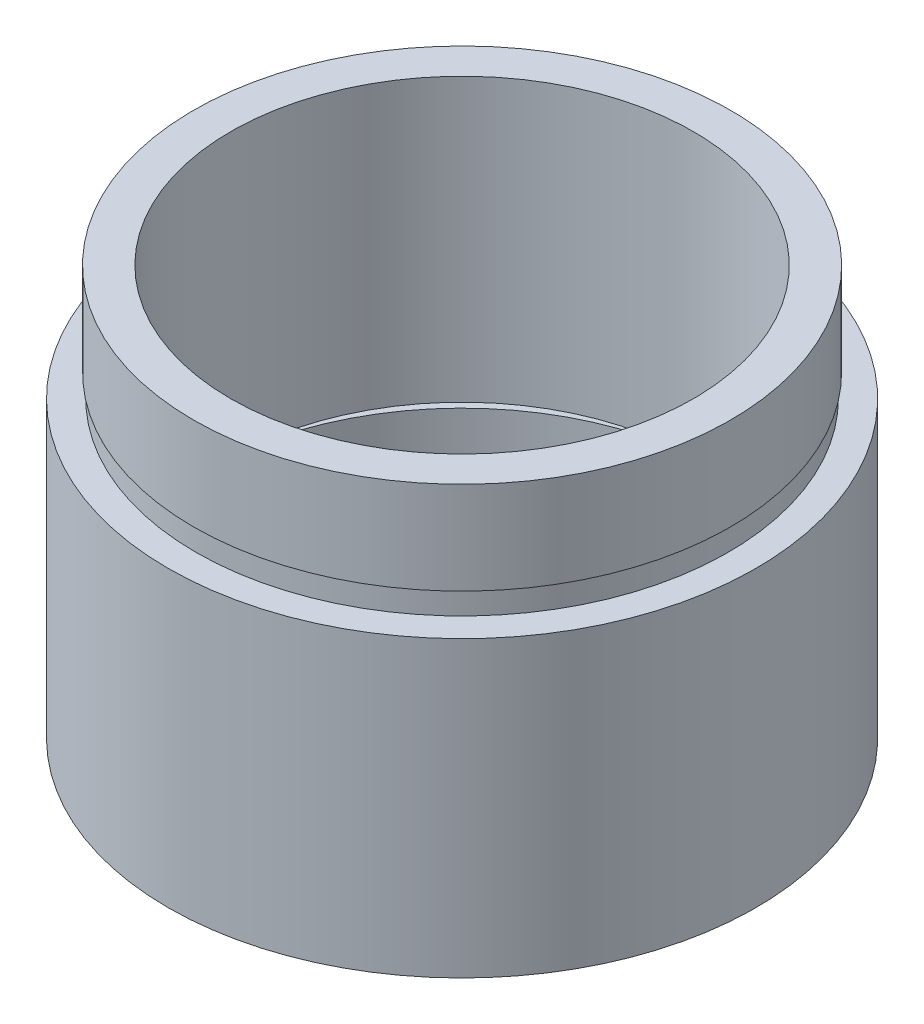
SolidWorks part; units mm, degrees
ref_plane "前视基准面" through (0, 0, 0) normal (0, 0, 1) x (1, 0, 0)
ref_plane "上视基准面" through (0, 0, 0) normal (0, 1, 0) x (1, 0, 0)
ref_plane "右视基准面" through (0, 0, 0) normal (1, 0, 0) x (0, 0, -1)
sketch "草图1" plane through (0, 0, 0) normal (0, 0, 1) x (1, 0, 0)
  line L0 (0, 161.3762) -> (0, 0) construction
  line L1 (141.7365, 0) -> (-131.7984, 0) construction
  line L2 (12.7, 0) -> (12.7, 12.7)
  line L3 (11.1, 4.5) -> (11.7, 4.5)
  line L4 (11.1, 0) -> (12.7, 0)
  line L5 (11.7, 4.5) -> (11.7, 5.5)
  line L6 (10, 5.5) -> (10, 17.7)
  line L7 (11.1, 4.5) -> (11.1, 0)
  line L8 (11.7, 5.5) -> (10, 5.5)
  line L9 (11.5, 13.7) -> (11.5, 12.7)
  line L10 (12.7, 12.7) -> (11.5, 12.7)
  line L11 (11.6, 13.7) -> (11.6, 17.7)
  line L12 (11.5, 13.7) -> (11.6, 13.7)
  line L13 (11.6, 17.7) -> (10, 17.7)
  dimension "D2" = 12.7
  dimension "D3" = 11.7
  dimension "D4" = 10
  dimension "D5" = 11.5
  dimension "D6" = 11.6
  dimension "D7" = 1
  dimension "D8" = 12.7
  dimension "D9" = 5
  dimension "D10" = 1
  dimension "D11" = 11.1
  dimension "D12" = 4.5
revolve "旋转1" add sketch "草图1" angle 360 about L0
cosmetic thread "装饰螺纹线1" parameters "D2"=23.2
cosmetic thread "装饰螺纹线2" parameters "D2"=21
cosmetic thread "装饰螺纹线3" parameters "D2"=23
